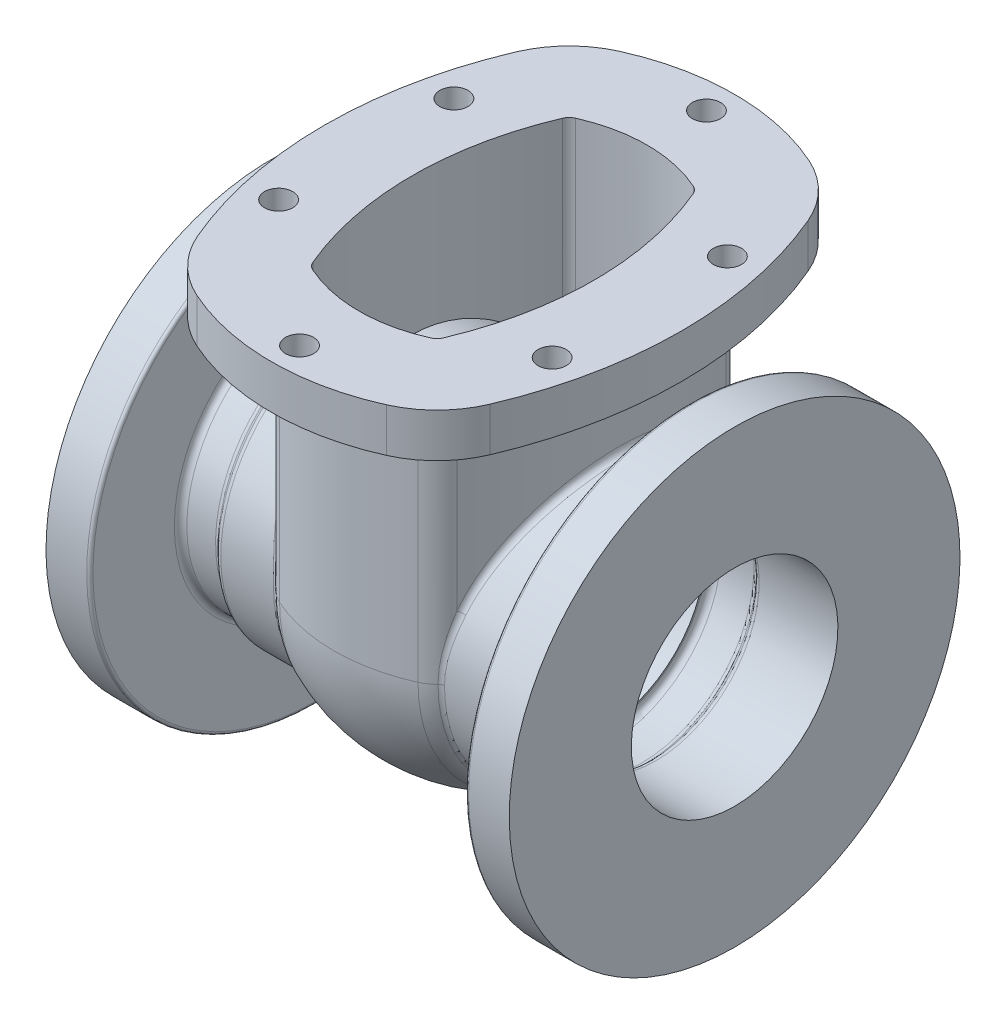
SolidWorks part; units mm, degrees
ref_plane "Front Plane" through (0, 0, 0) normal (0, 0, 1) x (1, 0, 0)
ref_plane "Top Plane" through (0, 0, 0) normal (0, 1, 0) x (1, 0, 0)
ref_plane "Right Plane" through (0, 0, 0) normal (1, 0, 0) x (0, 0, -1)
sketch "Sketch1" plane through (0, 0, 0) normal (0, 1, 0) x (1, 0, 0)
  line L0 (0, 73.025) -> (0, 0) construction
  line L1 (0, 0) -> (46.0375, 0) construction
  arc A0 (-29.9031, 66.6217) -> (29.9031, 66.6217) centre (0, 0) cw
  arc A1 (33.1473, -63.3113) -> (33.1473, 63.3113) centre (-115.8875, 0) ccw
  arc A2 (29.9031, 66.6217) -> (33.1473, 63.3113) centre (27.3028, 60.8285) cw
  arc A3 (-29.9031, 66.6217) -> (-33.1473, 63.3113) centre (-27.3028, 60.8285) ccw
  arc A4 (-33.1473, -63.3113) -> (-33.1473, 63.3113) centre (115.8875, 0) cw
  arc A5 (-29.9031, -66.6217) -> (-33.1473, -63.3113) centre (-27.3028, -60.8285) cw
  arc A6 (29.9031, -66.6217) -> (33.1473, -63.3113) centre (27.3028, -60.8285) ccw
  arc A7 (-29.9031, -66.6217) -> (29.9031, -66.6217) centre (0, 0) ccw
  arc A8 (-74.0588, -80.6909) -> (-74.0588, 80.6909) centre (115.8875, 0) cw
  arc A9 (-48.105, 107.1741) -> (-74.0588, 80.6909) centre (-27.3028, 60.8285) ccw
  arc A10 (-48.105, 107.1741) -> (48.105, 107.1741) centre (0, 0) cw
  arc A11 (48.105, 107.1741) -> (74.0588, 80.6909) centre (27.3028, 60.8285) cw
  arc A12 (74.0588, -80.6909) -> (74.0588, 80.6909) centre (-115.8875, 0) ccw
  arc A13 (48.105, -107.1741) -> (74.0588, -80.6909) centre (27.3028, -60.8285) ccw
  arc A14 (-48.105, -107.1741) -> (48.105, -107.1741) centre (0, 0) ccw
  arc A15 (-48.105, -107.1741) -> (-74.0588, -80.6909) centre (-27.3028, -60.8285) cw
  circle A16 centre (0, 103.1875) radius 7.1437
  arc A19 (69.3541, 44.45) -> (69.3541, -44.45) centre (-115.8875, 0) cw construction
  circle A20 centre (69.3541, 44.45) radius 7.1438
  circle A21 centre (69.3541, -44.45) radius 7.1438
  circle A22 centre (0, -103.1875) radius 7.1437
  circle A23 centre (-69.3541, 44.45) radius 7.1438
  arc A24 (-69.3541, 44.45) -> (-69.3541, -44.45) centre (115.8875, 0) ccw construction
  circle A25 centre (-69.3541, -44.45) radius 7.1438
  dimension "D1" = 73.025
  dimension "D2" = 161.925
  dimension "D4" = 6.35
  dimension "D6" = 103.1875
  dimension "D7" = 14.2875
  dimension "D8" = 190.5
  dimension "D3" = 115.8875
  dimension "D9" = 44.45
  dimension "D5" = 44.45
extrude "Boss-Extrude1" add sketch "Sketch1" along normal blind 22.225
sketch "Sketch3" plane through (0, 0, 0) normal (1, 0, 0) x (0, 0, -1)
  line L0 (-73.025, 0) -> (-73.025, -120.65)
  line L1 (-107.1741, 0) -> (-80.6909, 0) construction
  line L2 (0, 0) -> (0, -120.65) construction
  line L3 (-80.6909, 0) -> (80.6909, 0) construction
  line L4 (80.6909, 22.225) -> (-80.6909, 22.225) construction
  line L5 (73.025, 0) -> (73.025, -120.65)
  arc A0 (-73.025, -120.65) -> (73.025, -120.65) centre (0, -120.65) ccw
  circle A1 centre (0, -120.65) radius 51.5938
  dimension "D3" = 103.1875
  dimension "D1" = 142.875
  dimension "D2" = 73.025
sketch "Sketch4" plane through (0, 0, 0) normal (0, -1, 0) x (1, 0, 0)
  arc A0 (-29.9031, 66.6217) -> (-33.1473, 63.3113) centre (-27.3028, 60.8285) ccw construction
  arc A1 (-33.1473, 63.3113) -> (-33.1473, -63.3113) centre (115.8875, 0) ccw construction
  arc A2 (-33.1473, -63.3113) -> (-29.9031, -66.6217) centre (-27.3028, -60.8285) ccw construction
  arc A3 (29.9031, -66.6217) -> (33.1473, -63.3113) centre (27.3028, -60.8285) ccw construction
  arc A4 (-29.9031, -66.6217) -> (29.9031, -66.6217) centre (0, 0) ccw construction
  arc A5 (33.1473, -63.3113) -> (33.1473, 63.3113) centre (-115.8875, 0) ccw construction
  arc A6 (33.1473, 63.3113) -> (29.9031, 66.6217) centre (27.3028, 60.8285) ccw construction
  arc A7 (29.9031, 66.6217) -> (-29.9031, 66.6217) centre (0, 0) ccw construction
  arc A8 (-29.9031, 66.6217) -> (-33.1473, 63.3113) centre (-27.3028, 60.8285) ccw
  arc A9 (-33.1473, 63.3113) -> (-33.1473, -63.3113) centre (115.8875, 0) ccw
  arc A10 (-33.1473, -63.3113) -> (-29.9031, -66.6217) centre (-27.3028, -60.8285) ccw
  arc A11 (29.9031, -66.6217) -> (33.1473, -63.3113) centre (27.3028, -60.8285) ccw
  arc A12 (-29.9031, -66.6217) -> (29.9031, -66.6217) centre (0, 0) ccw
  arc A13 (33.1473, -63.3113) -> (33.1473, 63.3113) centre (-115.8875, 0) ccw
  arc A14 (33.1473, 63.3113) -> (29.9031, 66.6217) centre (27.3028, 60.8285) ccw
  arc A15 (29.9031, 66.6217) -> (-29.9031, 66.6217) centre (0, 0) ccw
  arc A16 (44.8363, -68.2769) -> (44.8363, 68.2769) centre (-115.8875, 0) ccw
  arc A17 (44.8363, 68.2769) -> (35.1036, 78.2081) centre (27.3028, 60.8285) ccw
  arc A18 (35.1036, 78.2081) -> (-35.1036, 78.2081) centre (0, 0) ccw
  arc A19 (-35.1036, 78.2081) -> (-44.8363, 68.2769) centre (-27.3028, 60.8285) ccw
  arc A20 (-44.8363, 68.2769) -> (-44.8363, -68.2769) centre (115.8875, 0) ccw
  arc A21 (-44.8363, -68.2769) -> (-35.1036, -78.2081) centre (-27.3028, -60.8285) ccw
  arc A22 (-35.1036, -78.2081) -> (35.1036, -78.2081) centre (0, 0) ccw
  arc A23 (35.1036, -78.2081) -> (44.8363, -68.2769) centre (27.3028, -60.8285) ccw
  dimension "D1" = 12.7
extrude "Boss-Extrude2" add sketch "Sketch4" along normal up to vertex (120.65 mm away) up to point (0, -120.65, 73.025)
sketch "Sketch5" plane through (0, -120.65, 0) normal (0, -1, 0) x (1, 0, 0)
  line L0 (58.7375, 0) -> (-58.7375, 0) construction
  line L1 (58.7375, 0) -> (46.0375, 0)
  line L2 (-46.0375, 0) -> (-58.7375, 0)
  arc A0 (44.8363, -68.2769) -> (44.8363, 68.2769) centre (-115.8875, 0) ccw construction
  arc A1 (-44.8363, 68.2769) -> (-44.8363, -68.2769) centre (115.8875, 0) ccw construction
  arc A2 (-29.9031, 66.6217) -> (-33.1473, 63.3113) centre (-27.3028, 60.8285) ccw construction
  arc A3 (-33.1473, 63.3113) -> (-33.1473, -63.3113) centre (115.8875, 0) ccw construction
  arc A4 (33.1473, -63.3113) -> (33.1473, 63.3113) centre (-115.8875, 0) ccw construction
  arc A5 (33.1473, 63.3113) -> (29.9031, 66.6217) centre (27.3028, 60.8285) ccw construction
  arc A6 (29.9031, 66.6217) -> (-29.9031, 66.6217) centre (0, 0) ccw construction
  arc A7 (-29.9031, 66.6217) -> (-33.1473, 63.3113) centre (-27.3028, 60.8285) ccw
  arc A8 (-33.1473, 63.3113) -> (-46.0375, 0) centre (115.8875, 0) ccw
  arc A9 (46.0375, 0) -> (33.1473, 63.3113) centre (-115.8875, 0) ccw
  arc A10 (35.1036, -78.2081) -> (44.8363, -68.2769) centre (27.3028, -60.8285) ccw
  arc A11 (44.8363, -68.2769) -> (44.8363, 68.2769) centre (-115.8875, 0) ccw
  arc A12 (44.8363, 68.2769) -> (35.1036, 78.2081) centre (27.3028, 60.8285) ccw
  arc A13 (35.1036, 78.2081) -> (-35.1036, 78.2081) centre (0, 0) ccw
  arc A14 (-35.1036, 78.2081) -> (-44.8363, 68.2769) centre (-27.3028, 60.8285) ccw
  arc A15 (-44.8363, 68.2769) -> (-44.8363, -68.2769) centre (115.8875, 0) ccw
  arc A16 (-44.8363, -68.2769) -> (-35.1036, -78.2081) centre (-27.3028, -60.8285) ccw
  arc A17 (-35.1036, -78.2081) -> (35.1036, -78.2081) centre (0, 0) ccw
  arc A19 (58.7375, 0) -> (44.8363, 68.2769) centre (-115.8875, 0) ccw
  arc A20 (44.8363, 68.2769) -> (35.1036, 78.2081) centre (27.3028, 60.8285) ccw
  arc A21 (35.1036, 78.2081) -> (-35.1036, 78.2081) centre (0, 0) ccw
  arc A22 (-35.1036, 78.2081) -> (-44.8363, 68.2769) centre (-27.3028, 60.8285) ccw
  arc A23 (-44.8363, 68.2769) -> (-58.7375, 0) centre (115.8875, 0) ccw
  arc A26 (33.1473, 63.3113) -> (29.9031, 66.6217) centre (27.3028, 60.8285) ccw
  arc A27 (29.9031, 66.6217) -> (-29.9031, 66.6217) centre (0, 0) ccw
  dimension "D1" = 0
revolve "Revolve1" add sketch "Sketch5" angle 180 about L0
sketch "Sketch6" plane through (0, 0, 0) normal (0, 0, 1) x (1, 0, 0)
  line L0 (0, -120.65) -> (117.475, -120.65) construction
  line L1 (-35.1036, -120.65) -> (35.1036, -120.65) construction
  line L2 (117.475, -234.95) -> (96.8375, -234.95)
  line L3 (95.25, -233.3625) -> (95.25, -188.9125)
  line L4 (95.25, -188.9125) -> (77.5151, -188.9125)
  line L5 (75.2701, -189.8424) -> (72.3674, -192.7451)
  line L6 (70.1224, -193.675) -> (41.9367, -193.675)
  line L7 (117.475, -234.95) -> (117.475, -173.0375)
  line L8 (117.475, -173.0375) -> (77.5151, -173.0375)
  line L9 (75.2701, -173.9674) -> (72.3674, -176.8701)
  line L10 (70.1224, -177.8) -> (49.1209, -177.8)
  line L11 (0, -120.65) -> (0, 0) construction
  line L12 (-48.105, 0) -> (48.105, 0) construction
  line L13 (-70.1224, -177.8) -> (-49.1209, -177.8)
  line L14 (-75.2701, -173.9674) -> (-72.3674, -176.8701)
  line L15 (-117.475, -173.0375) -> (-77.5151, -173.0375)
  line L16 (-117.475, -234.95) -> (-117.475, -173.0375)
  line L17 (-70.1224, -193.675) -> (-41.9367, -193.675)
  line L18 (-75.2701, -189.8424) -> (-72.3674, -192.7451)
  line L19 (-95.25, -188.9125) -> (-77.5151, -188.9125)
  line L20 (-95.25, -233.3625) -> (-95.25, -188.9125)
  line L21 (-117.475, -234.95) -> (-96.8375, -234.95)
  line L22 (41.9367, -193.675) -> (-41.9367, -193.675)
  line L23 (49.1209, -177.8) -> (-49.1209, -177.8)
  arc A0 (44.8363, -188.9269) -> (58.7375, -120.65) centre (-115.8875, -120.65) ccw construction
  arc A1 (-58.7375, -120.65) -> (-44.8363, -188.9269) centre (115.8875, -120.65) ccw construction
  arc A2 (-44.8363, -188.9269) -> (-35.1036, -198.8581) centre (-27.3028, -181.4785) ccw construction
  arc A3 (35.1036, -198.8581) -> (44.8363, -188.9269) centre (27.3028, -181.4785) ccw construction
  arc A4 (-58.7375, -120.65) -> (-44.8363, -188.9269) centre (115.8875, -120.65) ccw
  arc A5 (-44.8363, -188.9269) -> (-35.1036, -198.8581) centre (-27.3028, -181.4785) ccw
  arc A6 (44.8363, -188.9269) -> (58.7375, -120.65) centre (-115.8875, -120.65) ccw
  arc A7 (35.1036, -198.8581) -> (44.8363, -188.9269) centre (27.3028, -181.4785) ccw
  arc A8 (96.8375, -234.95) -> (95.25, -233.3625) centre (96.8375, -233.3625) cw
  arc A9 (77.5151, -173.0375) -> (75.2701, -173.9674) centre (77.5151, -176.2125) ccw
  arc A10 (72.3674, -176.8701) -> (70.1224, -177.8) centre (70.1224, -174.625) cw
  arc A11 (72.3674, -192.7451) -> (70.1224, -193.675) centre (70.1224, -190.5) cw
  arc A12 (77.5151, -188.9125) -> (75.2701, -189.8424) centre (77.5151, -192.0875) ccw
  arc A13 (-77.5151, -188.9125) -> (-75.2701, -189.8424) centre (-77.5151, -192.0875) cw
  arc A14 (-72.3674, -192.7451) -> (-70.1224, -193.675) centre (-70.1224, -190.5) ccw
  arc A15 (-72.3674, -176.8701) -> (-70.1224, -177.8) centre (-70.1224, -174.625) ccw
  arc A16 (-77.5151, -173.0375) -> (-75.2701, -173.9674) centre (-77.5151, -176.2125) cw
  arc A17 (-96.8375, -234.95) -> (-95.25, -233.3625) centre (-96.8375, -233.3625) ccw
  arc A18 (-35.1036, -198.8581) -> (-44.8363, -188.9269) centre (-27.3028, -181.4785) cw
  point P42 (95.25, -234.95)
  point P45 (76.2, -173.0375)
  point P48 (71.4375, -177.8)
  point P51 (71.4375, -193.675)
  point P54 (76.2, -188.9125)
  point P63 (-76.2, -188.9125)
  point P64 (-71.4375, -193.675)
  point P65 (-71.4375, -177.8)
  point P66 (-76.2, -173.0375)
  point P67 (-95.25, -234.95)
  dimension "D10" = 1.5875
  dimension "D11" = 3.175
  dimension "D2" = 114.3
  dimension "D3" = 22.225
  dimension "D4" = 19.05
  dimension "D5" = 15.875
  dimension "D6" = 45
  dimension "D7" = 4.7625
  dimension "D8" = 15.875
  dimension "D9" = 52.3875
  dimension "D12" = 117.475
revolve "Revolve2" add sketch "Sketch6" angle 360 about L0
extrude "Cut-Extrude3" cut sketch "Sketch3" against normal through all both and the other way through all
fillet "Fillet1" radius 3.175 4 edges at (58.5076, -64.2063, -8.9574) (-58.5076, -64.2063, -8.9574) (49.1209, -177.8, 0) (-49.1209, -177.8, 0)
sketch "Sketch10" plane through (0, 0, 0) normal (1, 0, 0) x (0, 0, -1)
  line L0 (73.025, -120.65) -> (-73.025, -120.65) construction
  circle A0 centre (0, -120.65) radius 73.025
  circle A1 centre (0, -120.65) radius 73.025 construction
  circle A2 centre (0, -120.65) radius 60.325
  dimension "D1" = 12.7
extrude "Boss-Extrude3" add sketch "Sketch10" against normal up to body and the other way up to body separate body
sketch "Sketch11" plane through (0, 0, 0) normal (0, 0, 1) x (1, 0, 0)
  line L0 (0, -206.375) -> (0, 22.225) construction
  line L1 (48.105, 22.225) -> (-48.105, 22.225) construction
  line L2 (19.2368, -191.0957) -> (37.8999, 22.225)
  line L3 (25.4, -120.65) -> (0, -120.65) construction
  line L4 (37.8999, 22.225) -> (-37.8999, 22.225)
  line L5 (-19.2368, -191.0957) -> (-37.8999, 22.225)
  arc A0 (-35.1036, -198.8581) -> (35.1036, -198.8581) centre (0, -120.65) ccw construction
  arc A1 (19.2368, -191.0957) -> (-19.2368, -191.0957) centre (0, -120.65) cw
  dimension "D4" = 73.025
  dimension "D1" = 142.875
  dimension "D2" = 25.4
  dimension "D3" = 5
extrude "Cut-Extrude4" [suppressed] cut sketch "Sketch11" against normal up to surface and the other way up to surface
ref_plane "Plane4" through (0, 15.875, 0) normal (0, 1, 0) x (1, 0, 0)
sketch "Sketch15" [suppressed] plane through (0, 15.875, 0) normal (0, 1, 0) x (1, 0, 0)
  line L0 (0, 73.025) -> (0, -73.025) construction
  line L1 (5.5563, 58.7375) -> (-5.5562, 58.7375)
  line L2 (-5.5562, 58.7375) -> (-6.35, 72.7484)
  line L3 (5.5563, 58.7375) -> (6.35, 72.7484)
  line L4 (-46.0375, 0) -> (46.0375, 0) construction
  line L5 (5.5562, -58.7375) -> (6.35, -72.7484)
  line L6 (-5.5563, -58.7375) -> (-6.35, -72.7484)
  line L7 (5.5562, -58.7375) -> (-5.5563, -58.7375)
  line L8 (-6.35, -72.7484) -> (-6.35, -74.3359)
  line L9 (-6.35, -74.3359) -> (6.35, -74.3359)
  line L10 (6.35, -74.3359) -> (6.35, -72.7484)
  line L11 (-6.35, 72.7484) -> (-6.35, 74.3359)
  line L12 (-6.35, 74.3359) -> (6.35, 74.3359)
  line L13 (6.35, 74.3359) -> (6.35, 72.7484)
  arc A0 (29.9031, 66.6217) -> (-29.9031, 66.6217) centre (0, 0) ccw construction
  arc A2 (-33.1473, 63.3113) -> (-33.1473, -63.3113) centre (115.8875, 0) ccw construction
  arc A4 (33.1473, -63.3113) -> (33.1473, 63.3113) centre (-115.8875, 0) ccw construction
  point P11 (0, 58.7375)
  point P23 (0, -58.7375)
  dimension "D1" = 5.5562
  dimension "D3" = 6.35
  dimension "D2" = 14.2875
  dimension "D4" = 1.5875
extrude "Boss-Extrude5" [suppressed] add sketch "Sketch15" against normal blind 146.05 contours L11 L12 L13 L3 L1 L2 | L10 L5 L7 L6 L8 L9
fillet "Fillet3" [suppressed] radius 1.5875
fillet "Fillet4" radius 3.175 10 edges at (-41.9367, -193.675, 0) (41.9367, -193.675, 0) (95.25, -188.9125, 0) (-95.25, -188.9125, 0) (-58.1888, -48.9471, -13.8328) (58.1888, -48.9471, -13.8328)
